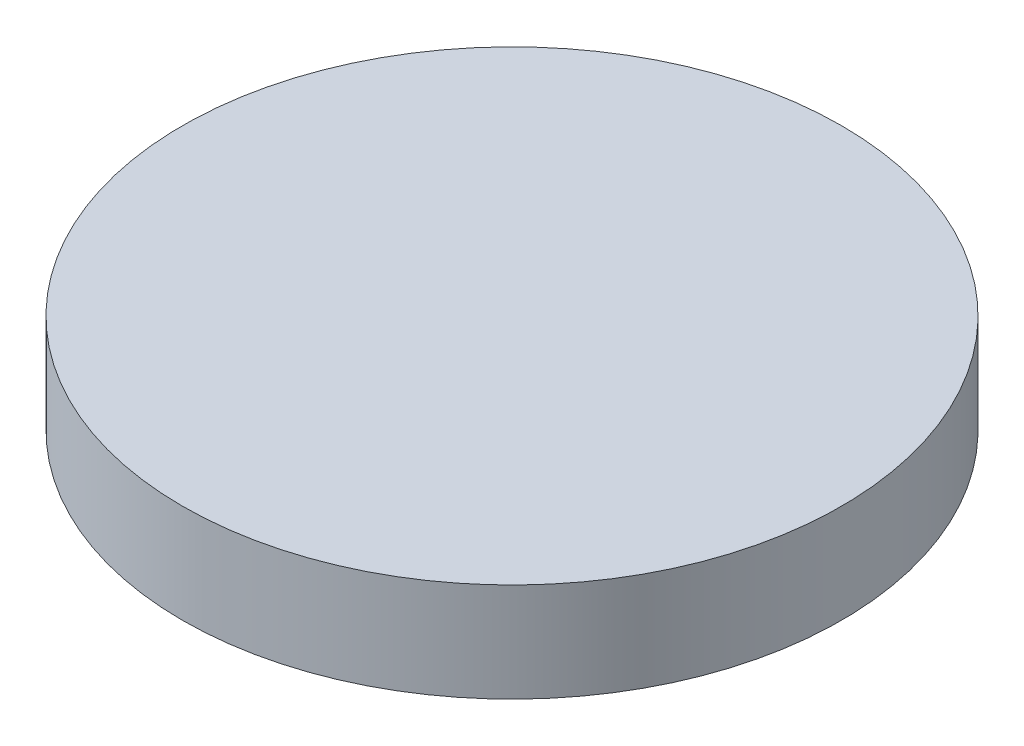
SolidWorks part; units mm, degrees
ref_plane "前视基准面" through (0, 0, 0) normal (0, 0, 1) x (1, 0, 0)
ref_plane "上视基准面" through (0, 0, 0) normal (0, 1, 0) x (1, 0, 0)
ref_plane "右视基准面" through (0, 0, 0) normal (1, 0, 0) x (0, 0, -1)
sketch "草图1" plane through (0, 0, 0) normal (0, 1, 0) x (1, 0, 0)
  circle A0 centre (0, 0) radius 127
  dimension "D1" = 254
extrude "凸台-拉伸1" add sketch "草图1" along normal blind 38.1
